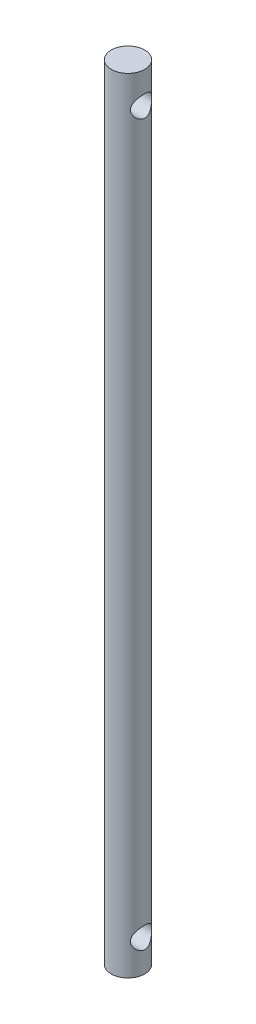
SolidWorks part; units mm, degrees
ref_plane "Front Plane" through (0, 0, 0) normal (0, 0, 1) x (1, 0, 0)
ref_plane "Top Plane" through (0, 0, 0) normal (0, 1, 0) x (1, 0, 0)
ref_plane "Right Plane" through (0, 0, 0) normal (1, 0, 0) x (0, 0, -1)
sketch "Sketch1" plane through (0, 0, 0) normal (0, 1, 0) x (1, 0, 0)
  circle A0 centre (0, 0) radius 1.5875
  dimension "D1" = 3.175
extrude "Boss-Extrude1" add sketch "Sketch1" along normal blind 74.2
sketch "Sketch2" plane through (0, 0, 0) normal (1, 0, 0) x (0, 0, -1)
  line L0 (-1.5875, 37.1) -> (1.5875, 37.1) construction
  line L1 (-1.5875, 74.2) -> (-1.5875, 0) construction
  line L2 (1.5875, 0) -> (1.5875, 74.2) construction
  line L3 (0, 74.2) -> (0, 0) construction
  line L4 (1.5875, 74.2) -> (-1.5875, 74.2) construction
  circle A0 centre (0, 71.2) radius 1
  circle A1 centre (0, 3) radius 1
  point P10 (0, 0)
  point P16 (0, 69.6091)
  dimension "D1" = 2
  dimension "D2" = 3
extrude "Cut-Extrude1" cut sketch "Sketch2" against normal up to next and the other way up to next
